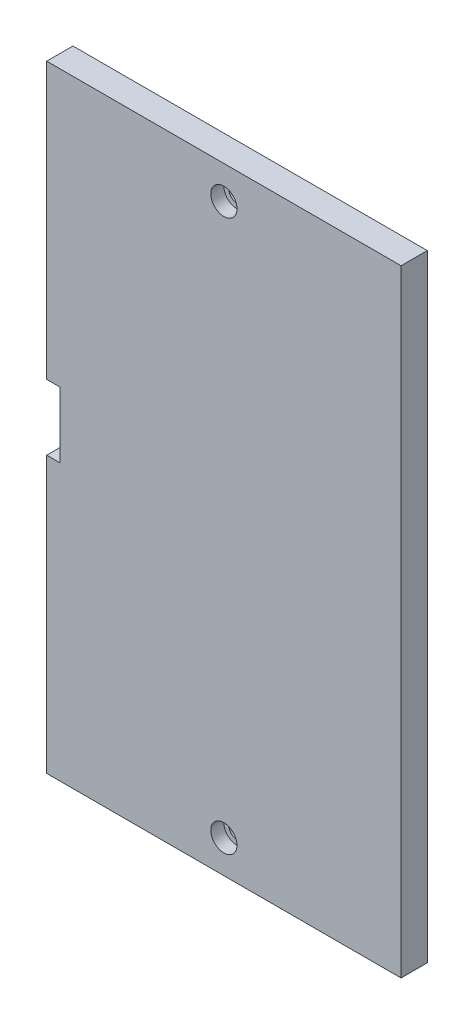
SolidWorks part; units mm, degrees
ref_plane "Front Plane" through (0, 0, 0) normal (0, 0, 1) x (1, 0, 0)
ref_plane "Top Plane" through (0, 0, 0) normal (0, 1, 0) x (1, 0, 0)
ref_plane "Right Plane" through (0, 0, 0) normal (1, 0, 0) x (0, 0, -1)
sketch "Sketch1" plane through (0, 0, 0) normal (0, 0, 1) x (1, 0, 0)
  line L1 (0, 0) -> (54, 0)
  line L2 (0, 0) -> (0, 94)
  line L3 (0, 94) -> (54, 94)
  line L4 (54, 0) -> (54, 94)
  line L5 (0, 0) -> (54, 94) construction
  line L6 (0, 94) -> (54, 0) construction
  point P4 (27, 47)
  dimension "D1" = 94
  dimension "D2" = 54
extrude "Boss-Extrude1" add sketch "Sketch1" along normal blind 4
sketch "Sketch2" plane through (0, 0, 4) normal (0, 0, 1) x (1, 0, 0)
  line L0 (-39.4614, 47) -> (103.5664, 47) construction
  line L1 (0, 0) -> (54, 0) construction
  line L2 (0, 52) -> (2, 52)
  line L3 (0, 94) -> (0, 0) construction
  line L4 (2, 52) -> (2, 42)
  line L5 (2, 42) -> (0, 42)
  line L6 (0, 42) -> (0, 52)
  dimension "D1" = 47
  dimension "D2" = 10
  dimension "D3" = 5
  dimension "D4" = 2
extrude "Cut-Extrude1" cut sketch "Sketch2" against normal up to next
sketch "Sketch3" plane through (0, 0, 4) normal (0, 0, 1) x (1, 0, 0)
  line L0 (27, 122.0259) -> (27, -18.8203) construction
  line L1 (0, 94) -> (0, 52) construction
  line L2 (54, 94) -> (0, 94) construction
  line L3 (0, 0) -> (54, 0) construction
  circle A0 centre (27, 89) radius 1.25
  circle A1 centre (27, 5) radius 1.25
  dimension "D3" = 2.5
  dimension "D5" = 2.5
  dimension "D1" = 27
  dimension "D2" = 5
  dimension "D4" = 5
extrude "Cut-Extrude2" cut sketch "Sketch3" against normal through all
sketch "Sketch4" plane through (0, 0, 4) normal (0, 0, 1) x (1, 0, 0)
  circle A0 centre (27, 89) radius 2
  circle A1 centre (27, 5) radius 2
  dimension "D1" = 4
  dimension "D2" = 4
chamfer "Chamfer1" distance 1 angle 45 1 edges at (2, 47, 0)
extrude "Cut-Extrude3" cut sketch "Sketch4" against normal blind 2
